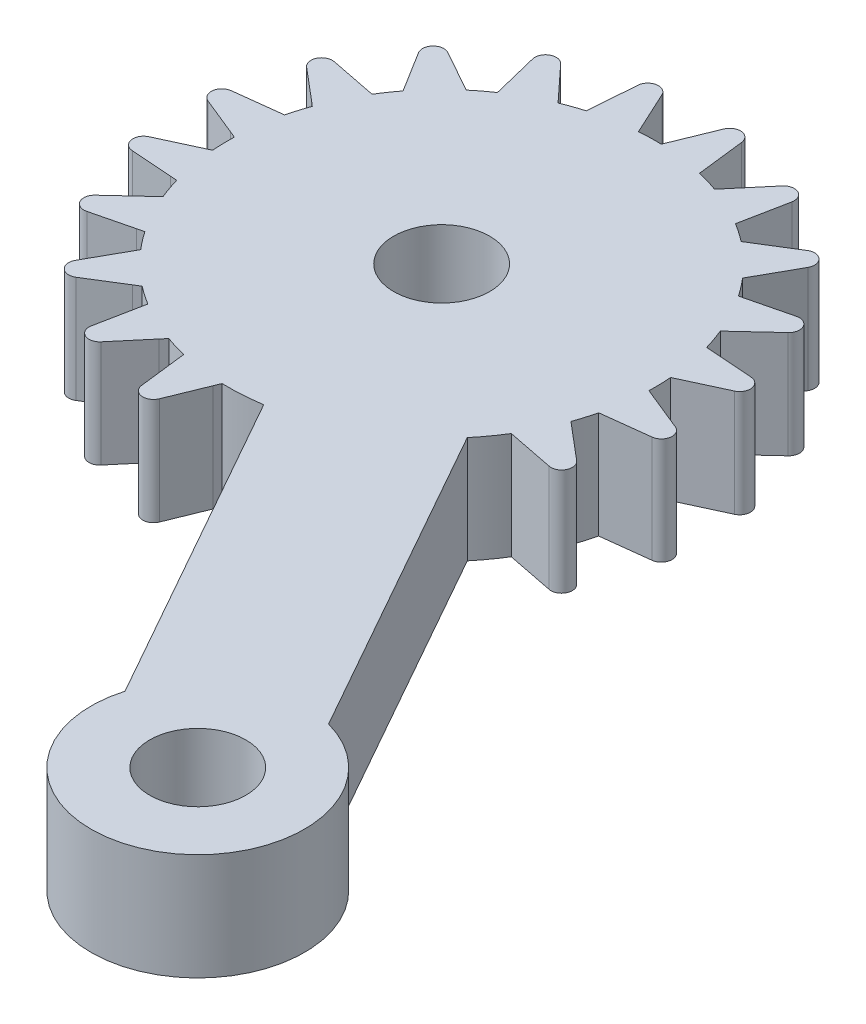
SolidWorks part; units mm, degrees
ref_plane "Front Plane" through (0, 0, 0) normal (0, 0, 1) x (1, 0, 0)
ref_plane "Top Plane" through (0, 0, 0) normal (0, 1, 0) x (1, 0, 0)
ref_plane "Right Plane" through (0, 0, 0) normal (1, 0, 0) x (0, 0, -1)
ref_plane "Plane1" through (0, -74, 0) normal (0, 1, 0) x (1, 0, 0)
sketch "Sketch1" plane through (0, -74, 0) normal (0, 1, 0) x (1, 0, 0)
  line L0 (9.7929, -22.0237) -> (18.164, -36.8907)
  line L1 (24.2635, -33.4563) -> (15.8924, -18.5892)
  line L2 (16.7571, -17.3948) -> (18.9657, -17.8316)
  line L3 (19.3799, -16.9546) -> (17.9109, -15.7157)
  line L4 (17.9109, -15.7157) -> (17.6649, -15.5048)
  line L5 (17.9632, -14.5079) -> (20.1986, -14.2408)
  line L6 (20.3216, -13.2787) -> (18.5416, -12.5544)
  line L7 (18.5416, -12.5544) -> (18.2425, -12.4299)
  line L8 (18.2181, -11.3896) -> (20.2616, -10.4448)
  line L9 (20.0813, -9.4918) -> (18.1646, -9.353)
  line L10 (18.1646, -9.353) -> (17.8416, -9.327)
  line L11 (17.497, -8.3452) -> (19.1485, -6.8151)
  line L12 (18.6825, -5.9645) -> (16.8167, -6.4248)
  line L13 (16.8167, -6.4248) -> (16.5015, -6.4998)
  line L14 (15.8704, -5.6726) -> (16.9682, -3.707)
  line L15 (16.2622, -3.0421) -> (14.6299, -4.0564)
  line L16 (14.6299, -4.0564) -> (14.3534, -4.2252)
  line L17 (13.4975, -3.6334) -> (13.9342, -1.4248)
  line L18 (13.0572, -1.0106) -> (11.8183, -2.4796)
  line L19 (11.8183, -2.4796) -> (11.6075, -2.7256)
  line L20 (10.6106, -2.4274) -> (10.3435, -0.1919)
  line L21 (9.3814, -0.069) -> (8.6571, -1.8489)
  line L22 (8.6571, -1.8489) -> (8.5326, -2.148)
  line L23 (7.4923, -2.1724) -> (6.5475, -0.1289)
  line L24 (5.5945, -0.3093) -> (5.4557, -2.226)
  line L25 (5.4557, -2.226) -> (5.4297, -2.5489)
  line L26 (4.4479, -2.8936) -> (2.9178, -1.242)
  line L27 (2.0672, -1.7081) -> (2.5274, -3.5738)
  line L28 (2.5274, -3.5738) -> (2.6025, -3.889)
  line L29 (1.7753, -4.5202) -> (-0.1903, -3.4223)
  line L30 (-0.8552, -4.1284) -> (0.159, -5.7606)
  line L31 (0.159, -5.7606) -> (0.3278, -6.0371)
  line L32 (-0.2639, -6.8931) -> (-2.4725, -6.4563)
  line L33 (-2.8867, -7.3333) -> (-1.4177, -8.5722)
  line L34 (-1.4177, -8.5722) -> (-1.1717, -8.7831)
  line L35 (-1.47, -9.78) -> (-3.7054, -10.0471)
  line L36 (-3.8284, -11.0091) -> (-2.0484, -11.7335)
  line L37 (-2.0484, -11.7335) -> (-1.7493, -11.858)
  line L38 (-1.7249, -12.8982) -> (-3.7684, -13.8431)
  line L39 (-3.588, -14.796) -> (-1.6714, -14.9349)
  line L40 (-1.6714, -14.9349) -> (-1.3484, -14.9609)
  line L41 (-1.0038, -15.9427) -> (-2.6553, -17.4728)
  line L42 (-2.1893, -18.3234) -> (-0.3235, -17.8631)
  line L43 (-0.3235, -17.8631) -> (-0.0083, -17.788)
  line L44 (0.6228, -18.6153) -> (-0.475, -20.5808)
  line L45 (0.231, -21.2458) -> (1.8633, -20.2315)
  line L46 (1.8633, -20.2315) -> (2.1398, -20.0627)
  line L47 (2.9957, -20.6544) -> (2.559, -22.863)
  line L48 (3.436, -23.2772) -> (4.6749, -21.8082)
  line L49 (4.6749, -21.8082) -> (4.8857, -21.5622)
  line L50 (5.8826, -21.8605) -> (6.1497, -24.096)
  line L51 (7.1118, -24.2189) -> (7.8361, -22.4389)
  line L52 (7.8361, -22.4389) -> (7.9606, -22.1398)
  arc A0 (18.164, -36.8907) -> (24.2635, -33.4563) centre (22.9657, -38.2849) ccw
  arc A1 (15.8924, -18.5892) -> (16.7571, -17.3948) centre (8.2466, -12.1439) ccw
  arc A2 (18.9657, -17.8316) -> (19.3799, -16.9546) centre (19.0627, -17.3411) ccw
  arc A3 (17.6649, -15.5048) -> (17.9632, -14.5079) centre (8.2466, -12.1439) ccw
  arc A4 (20.1986, -14.2408) -> (20.3216, -13.2787) centre (20.1393, -13.7443) ccw
  arc A5 (18.2425, -12.4299) -> (18.2181, -11.3896) centre (8.2466, -12.1439) ccw
  arc A6 (20.2616, -10.4448) -> (20.0813, -9.4918) centre (20.0518, -9.991) ccw
  arc A7 (17.8416, -9.327) -> (17.497, -8.3452) centre (8.2466, -12.1439) ccw
  arc A8 (19.1485, -6.8151) -> (18.6825, -5.9645) centre (18.8087, -6.4483) ccw
  arc A9 (16.5015, -6.4998) -> (15.8704, -5.6726) centre (8.2466, -12.1439) ccw
  arc A10 (16.9682, -3.707) -> (16.2622, -3.0421) centre (16.5317, -3.4632) ccw
  arc A11 (14.3534, -4.2252) -> (13.4975, -3.6334) centre (8.2466, -12.1439) ccw
  arc A12 (13.9342, -1.4248) -> (13.0572, -1.0106) centre (13.4437, -1.3278) ccw
  arc A13 (11.6075, -2.7256) -> (10.6106, -2.4274) centre (8.2466, -12.1439) ccw
  arc A14 (10.3435, -0.1919) -> (9.3814, -0.069) centre (9.847, -0.2512) ccw
  arc A15 (8.5326, -2.148) -> (7.4923, -2.1724) centre (8.2466, -12.1439) ccw
  arc A16 (6.5475, -0.1289) -> (5.5945, -0.3093) centre (6.0936, -0.3387) ccw
  arc A17 (5.4297, -2.5489) -> (4.4479, -2.8936) centre (8.2466, -12.1439) ccw
  arc A18 (2.9178, -1.242) -> (2.0672, -1.7081) centre (2.551, -1.5818) ccw
  arc A19 (2.6025, -3.889) -> (1.7753, -4.5202) centre (8.2466, -12.1439) ccw
  arc A20 (-0.1903, -3.4223) -> (-0.8552, -4.1284) centre (-0.4341, -3.8588) ccw
  arc A21 (0.3278, -6.0371) -> (-0.2639, -6.8931) centre (8.2466, -12.1439) ccw
  arc A22 (-2.4725, -6.4563) -> (-2.8867, -7.3333) centre (-2.5695, -6.9468) ccw
  arc A23 (-1.1717, -8.7831) -> (-1.47, -9.78) centre (8.2466, -12.1439) ccw
  arc A24 (-3.7054, -10.0471) -> (-3.8284, -11.0091) centre (-3.6461, -10.5435) ccw
  arc A25 (-1.7493, -11.858) -> (-1.7249, -12.8982) centre (8.2466, -12.1439) ccw
  arc A26 (-3.7684, -13.8431) -> (-3.588, -14.796) centre (-3.5586, -14.2969) ccw
  arc A27 (-1.3484, -14.9609) -> (-1.0038, -15.9427) centre (8.2466, -12.1439) ccw
  arc A28 (-2.6553, -17.4728) -> (-2.1893, -18.3234) centre (-2.3155, -17.8395) ccw
  arc A29 (-0.0083, -17.788) -> (0.6228, -18.6153) centre (8.2466, -12.1439) ccw
  arc A30 (-0.475, -20.5808) -> (0.231, -21.2458) centre (-0.0385, -20.8247) ccw
  arc A31 (2.1398, -20.0627) -> (2.9957, -20.6544) centre (8.2466, -12.1439) ccw
  arc A32 (2.559, -22.863) -> (3.436, -23.2772) centre (3.0495, -22.96) ccw
  arc A33 (4.8857, -21.5622) -> (5.8826, -21.8605) centre (8.2466, -12.1439) ccw
  arc A34 (6.1497, -24.096) -> (7.1118, -24.2189) centre (6.6462, -24.0367) ccw
  arc A35 (7.9606, -22.1398) -> (9.7929, -22.0237) centre (8.2466, -12.1439) ccw
  dimension "D2" = 5
  dimension "D1" = 30
extrude "Boss-Extrude1" add sketch "Sketch1" against normal blind 5
ref_plane "Plane2" through (0, 0, 12.1439) normal (0, 0, 1) x (1, 0, 0)
hole_wizard "Ø4.5 (4.5) Diameter Hole1" positions "Sketch5" profile "Sketch4" hole size "Ø4.5" standard "ANSI Metric" end condition through all
sketch "Sketch5" plane through (0, -79, 0) normal (0, -1, 0) x (-1, 0, 0)
  point P0 (-22.9657, -38.2849)
  point P1 (-8.2466, -12.1439)
sketch "Sketch4" plane through (22.9657, -79, 38.2849) normal (1, 0, 0) x (0, 0, -1)
  line L0 (0, 0) -> (0, 5)
  line L1 (0, 5) -> (2.25, 5)
  line L2 (2.25, 5) -> (2.25, 0)
  line L5 (2.25, 0) -> (0, 0)
  line L11 (0, -6.35) -> (0, 107.95) construction
  dimension "Thru Hole Dia." = 4.5
  dimension "Thru Hole Depth" = 5
